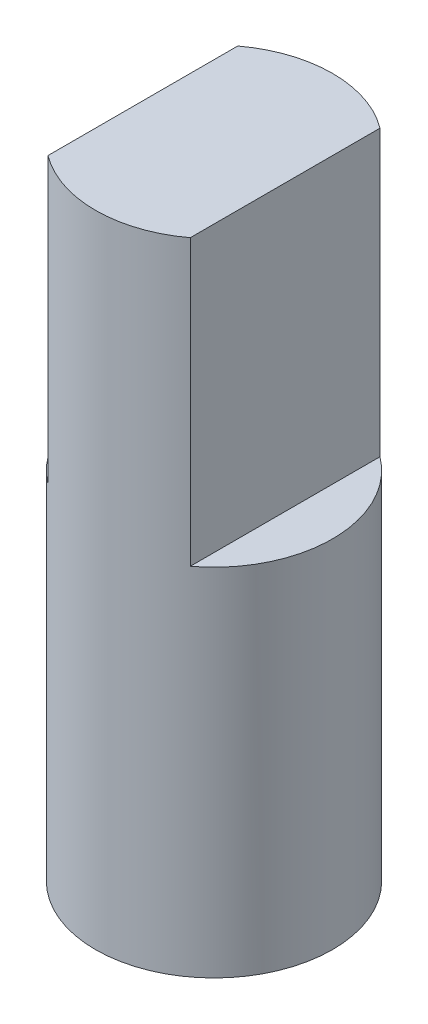
SolidWorks part; units mm, degrees
ref_plane "Alzado" through (0, 0, 0) normal (0, 0, 1) x (1, 0, 0)
ref_plane "Planta" through (0, 0, 0) normal (0, 1, 0) x (1, 0, 0)
ref_plane "Vista lateral" through (0, 0, 0) normal (1, 0, 0) x (0, 0, -1)
sketch "Croquis1" plane through (0, 0, 0) normal (0, 1, 0) x (1, 0, 0)
  line L0 (0, 0) -> (14, 0)
  line L2 (2.8442, -7.3) -> (17, -7.3)
  line L3 (2.8442, -7.3) -> (2.8442, 7.3)
  line L4 (2.8442, 7.3) -> (17, 7.3)
  line L5 (17, -7.3) -> (17, 7.3)
  line L6 (2.8442, -7.3) -> (17, 7.3) construction
  line L7 (2.8442, 7.3) -> (17, -7.3) construction
  circle A0 centre (0, 0) radius 14
  point P3 (9.9221, 0)
  dimension "D1" = 28
  dimension "D2" = 17
  dimension "D3" = 14.6
extrude "Saliente-Extruir1" add sketch "Croquis1" along normal blind 19
sketch "Croquis2" plane through (0, 19, 0) normal (0, 1, 0) x (1, 0, 0)
  circle A0 centre (-8, 0) radius 4.5
  dimension "D1" = 9
extrude "Saliente-Extruir2" add sketch "Croquis2" along normal blind 1.5
sketch "Croquis3" plane through (0, 20.5, 0) normal (0, 1, 0) x (1, 0, 0)
  circle A0 centre (-8, 0) radius 2.5
  dimension "D1" = 5
extrude "Saliente-Extruir3" add sketch "Croquis3" along normal blind 2.5
sketch "Croquis4" plane through (0, 23, 0) normal (0, 1, 0) x (1, 0, 0)
  line L1 (-9.5, -3.4931) -> (-6.5, -3.4931)
  line L2 (-9.5, -3.4931) -> (-9.5, 3.4931)
  line L3 (-9.5, 3.4931) -> (-6.5, 3.4931)
  line L4 (-6.5, -3.4931) -> (-6.5, 3.4931)
  line L5 (-9.5, -3.4931) -> (-6.5, 3.4931) construction
  line L6 (-9.5, 3.4931) -> (-6.5, -3.4931) construction
  circle A0 centre (-8, 0) radius 2.5
  circle M2 centre (-8, 0) radius 2.5
  dimension "D1" = 3
extrude "Saliente-Extruir4" add sketch "Croquis4" along normal blind 6 contours L4 L2 M2
sketch "Croquis5" plane through (17, 0, 0) normal (1, 0, 0) x (0, 0, -1)
  line L1 (-14, 19) -> (14, 19)
  line L2 (-14, 19) -> (-14, 0)
  line L3 (-14, 0) -> (14, 0)
  line L4 (14, 19) -> (14, 0)
  line L5 (-14, 19) -> (4.5, 19)
  line L6 (-14, 19) -> (-14, 20.5)
  line L7 (-14, 20.5) -> (4.5, 20.5)
  line L8 (4.5, 19) -> (4.5, 20.5)
extrude "Cortar-Extruir3" cut sketch "Croquis5" against normal blind 50 contours L1 L8 L7 L6
sketch "Croquis6" plane through (0, 20.5, 0) normal (0, -1, 0) x (1, 0, 0)
  circle A0 centre (-8, 0) radius 2.5
extrude "Saliente-Extruir5" add sketch "Croquis6" along normal blind 5
